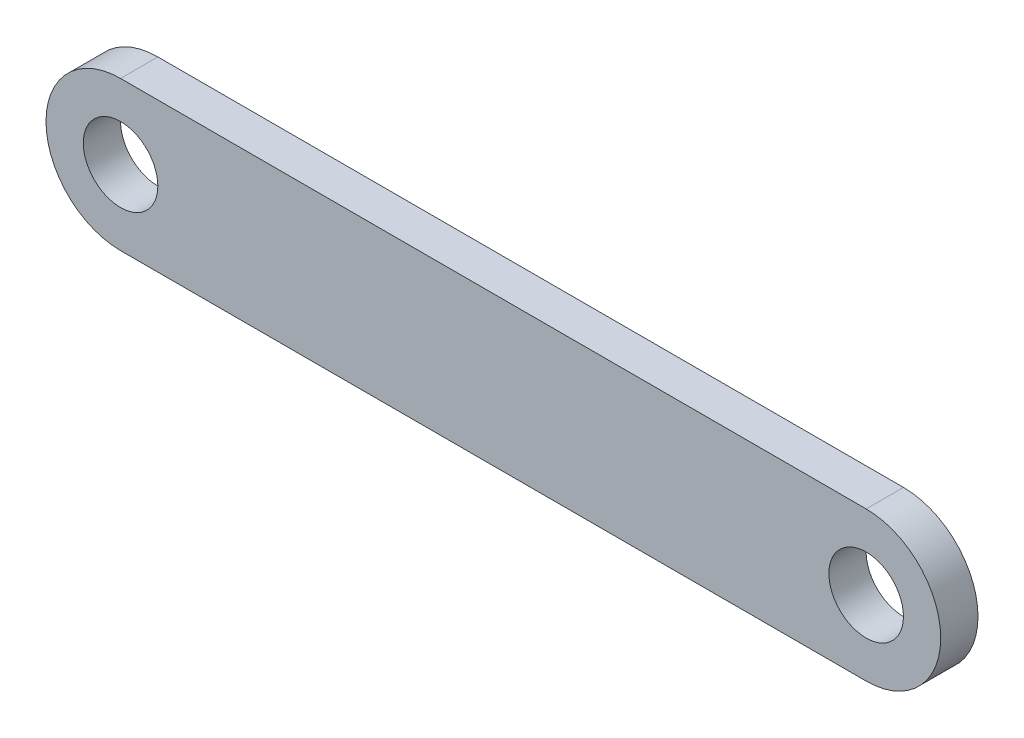
SolidWorks part; units mm, degrees
ref_plane "Front Plane" through (0, 0, 0) normal (0, 0, 1) x (1, 0, 0)
ref_plane "Top Plane" through (0, 0, 0) normal (0, 1, 0) x (1, 0, 0)
ref_plane "Right Plane" through (0, 0, 0) normal (1, 0, 0) x (0, 0, -1)
sketch "Sketch1" plane through (0, 0, 0) normal (0, 0, 1) x (1, 0, 0)
  line L0 (-50, 0) -> (50, 0) construction
  line L3 (-50, 10) -> (50, 10)
  line L4 (-50, -10) -> (50, -10)
  arc A2 (-50, 10) -> (-50, -10) centre (-50, 0) ccw
  arc A3 (50, -10) -> (50, 10) centre (50, 0) ccw
  circle A4 centre (-50, 0) radius 5
  circle A5 centre (50, 0) radius 5
  point P2 (0, 0)
  dimension "D3" = 10
  dimension "D1" = 100
  dimension "D2" = 20
extrude "Boss-Extrude1" add sketch "Sketch1" along normal blind 5
